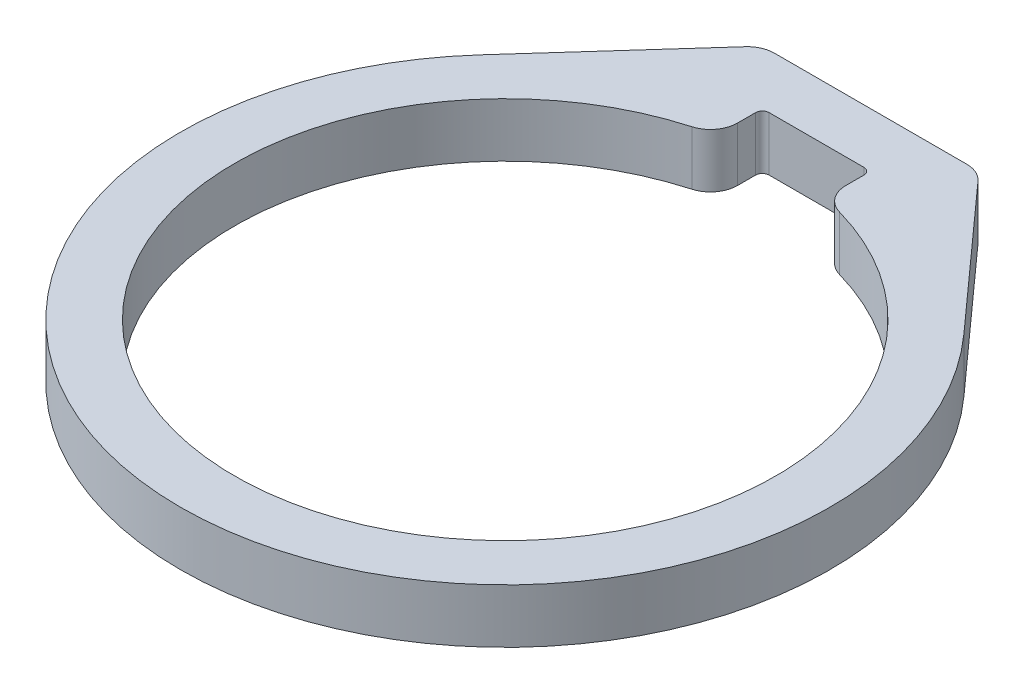
SolidWorks part; units mm, degrees
material "6061-T6 (SS)"
ref_plane "Front Plane" through (0, 0, 0) normal (0, 0, 1) x (1, 0, 0)
ref_plane "Top Plane" through (0, 0, 0) normal (0, 1, 0) x (1, 0, 0)
ref_plane "Right Plane" through (0, 0, 0) normal (1, 0, 0) x (0, 0, -1)
sketch "Sketch1" plane through (0, 0, 0) normal (0, 1, 0) x (1, 0, 0)
  line L0 (0, 0) -> (0, 77.2217) construction
  line L1 (-12.7, 42.8625) -> (-28.334, 25.4714)
  line L2 (-6.35, 36.5125) -> (6.35, 36.5125)
  line L3 (-6.35, 36.5125) -> (-6.35, 31.1085)
  line L5 (6.35, 36.5125) -> (6.35, 31.1085)
  line L6 (12.7, 42.8625) -> (28.334, 25.4714)
  line L8 (-12.7, 42.8625) -> (12.7, 42.8625)
  line L12 (-12.7, 42.8625) -> (0, 31.75) construction
  line L13 (0, 31.75) -> (12.7, 42.8625) construction
  arc A0 (-6.35, 31.1085) -> (6.35, 31.1085) centre (0, 0) ccw
  arc A1 (-28.334, 25.4714) -> (28.334, 25.4714) centre (0, 0) ccw
  point P4 (0, 31.75)
  point P5 (0, 31.75)
  dimension "D1" = 63.5
  dimension "D2" = 76.2
  dimension "D3" = 36.5125
  dimension "D4" = 42.8625
  dimension "D5" = 12.7
  dimension "D6" = 25.4
  dimension "D7" = 6.35
  dimension "D8" = 12.7
extrude "Boss-Extrude1" add sketch "Sketch1" along normal blind 6.35
fillet "Fillet1" radius 0.7937 2 edges at (6.35, 3.175, -36.5125) (-6.35, 3.175, -36.5125)
fillet "Fillet3" radius 3.175 4 edges at (6.35, 3.175, -31.1085) (-6.35, 3.175, -31.1085) (12.7, 3.175, -42.8625) (-12.7, 3.175, -42.8625)
